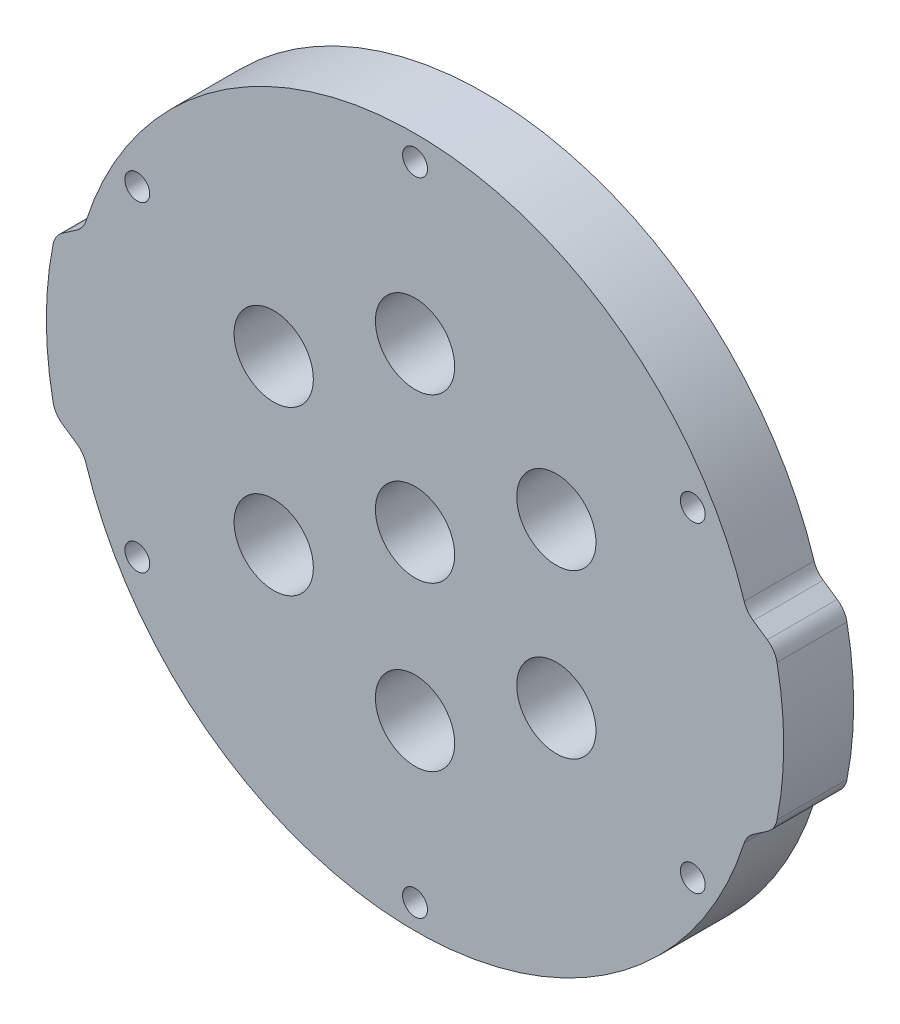
SolidWorks part; units mm, degrees
material "ABS PC"
ref_plane "Front Plane" through (0, 0, 0) normal (0, 0, 1) x (1, 0, 0)
ref_plane "Top Plane" through (0, 0, 0) normal (0, 1, 0) x (1, 0, 0)
ref_plane "Right Plane" through (0, 0, 0) normal (1, 0, 0) x (0, 0, -1)
sketch "Sketch1" plane through (0, 0, 0) normal (0, 0, 1) x (1, 0, 0)
  line L0 (-46.3248, 10) -> (-42.6562, 12.5)
  line L1 (-46.3248, -10) -> (-42.6562, -12.5)
  line L2 (46.3248, 10) -> (42.6562, 12.5)
  line L3 (46.3248, -10) -> (42.6562, -12.5)
  line L4 (0, 0) -> (35.7452, 20.6375) construction
  line L5 (35.7452, 20.6375) -> (38.4948, 22.225) construction
  line L6 (0, 41.275) -> (0, 0) construction
  line L7 (-47.5, 0) -> (0, 0) construction
  line L8 (0, 0) -> (47.5, 0) construction
  arc A0 (-42.6562, -12.5) -> (42.6562, -12.5) centre (0, 0) ccw
  circle A1 centre (0, 41.275) radius 1.6
  circle A2 centre (35.7452, 20.6375) radius 1.6
  circle A3 centre (35.7452, -20.6375) radius 1.6
  circle A4 centre (0, -41.275) radius 1.6
  circle A5 centre (-35.7452, -20.6375) radius 1.6
  circle A6 centre (-35.7452, 20.6375) radius 1.6
  arc A7 (-46.3248, 10) -> (-46.3248, -10) centre (-2.45, 0) ccw
  arc A8 (46.3248, 10) -> (46.3248, -10) centre (2.45, 0) cw
  arc A9 (42.6562, 12.5) -> (-42.6562, 12.5) centre (0, 0) ccw
  circle A10 centre (-47.5, 0) radius 1.6 construction
  circle A11 centre (-47.5, 0) radius 2.5 construction
  arc A12 (-42.6562, 12.5) -> (-42.6562, -12.5) centre (0, 0) ccw construction
  circle A13 centre (47.5, 0) radius 1.6 construction
  point P17 (0, 0)
  point P19 (-47.45, 0)
  dimension "D1" = 88.9
  dimension "D2" = 3.175
  dimension "D3" = 3.2
  dimension "D6" = 3
  dimension "D11" = 3.2
  dimension "D12" = 5
  dimension "D14" = 45
  dimension "D5" = 25
  dimension "D7" = 20
  dimension "D9" = 3.175
  dimension "D10" = 60
  dimension "D13" = 47.5
  dimension "D4" = 6
extrude "Boss-Extrude1" add sketch "Sketch1" along normal blind 9
fillet "Fillet1" radius 3 8 edges at (42.6562, 12.5, 4.5) (42.6562, -12.5, 4.5) (-42.6562, -12.5, 4.5) (-46.3248, -10, 4.5) (-42.6562, 12.5, 4.5) (-46.3248, 10, 4.5) (46.3248, -10, 4.5) (46.3248, 10, 4.5)
sketch "Sketch2" plane through (0, 0, 9) normal (0, 0, 1) x (1, 0, 0)
  line L0 (0, 0) -> (0, 21) construction
  circle A0 centre (0, 0) radius 31.75 construction
  circle A1 centre (0, 21) radius 5.1
  circle A2 centre (0, 21) radius 9 construction
  circle A3 centre (18.1865, 10.5) radius 5.1
  circle A4 centre (18.1865, 10.5) radius 9 construction
  circle A5 centre (18.1865, -10.5) radius 5.1
  circle A6 centre (18.1865, -10.5) radius 9 construction
  circle A7 centre (0, -21) radius 5.1
  circle A8 centre (0, -21) radius 9 construction
  circle A9 centre (-18.1865, -10.5) radius 5.1
  circle A10 centre (-18.1865, -10.5) radius 9 construction
  circle A11 centre (-18.1865, 10.5) radius 5.1
  circle A12 centre (-18.1865, 10.5) radius 9 construction
  circle A13 centre (0, 0) radius 5.1
  circle A14 centre (0, 0) radius 9 construction
  point P23 (0, 0)
  dimension "D1" = 63.5
  dimension "D2" = 10.2
  dimension "D3" = 18
  dimension "D5" = 21
  dimension "D4" = 6
extrude "Cut-Extrude1" cut sketch "Sketch2" against normal through all
